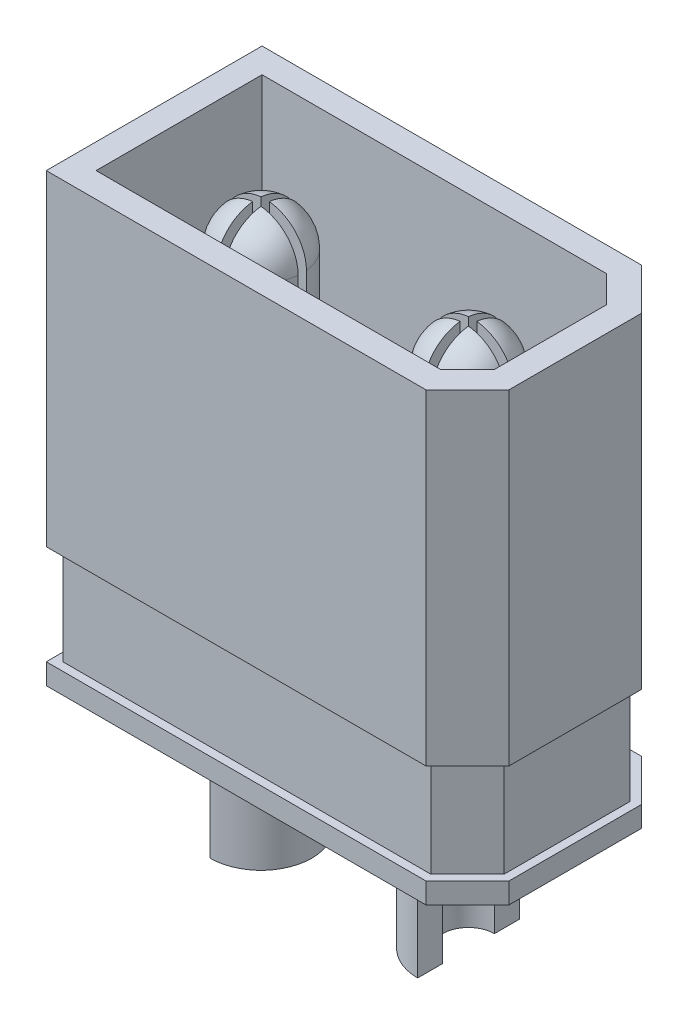
SolidWorks part; units mm, degrees
ref_plane "Front Plane" through (0, 0, 0) normal (0, 0, 1) x (1, 0, 0)
ref_plane "Top Plane" through (0, 0, 0) normal (0, 1, 0) x (1, 0, 0)
ref_plane "Right Plane" through (0, 0, 0) normal (1, 0, 0) x (0, 0, -1)
sketch "Sketch1" plane through (0, 0, 0) normal (0, 1, 0) x (1, 0, 0)
  line L0 (5.075, 1.6) -> (4.075, 2.6)
  line L1 (-5.075, 2.6) -> (5.075, 2.6)
  line L2 (-5.075, 2.6) -> (-5.075, -2.6)
  line L3 (-5.075, -2.6) -> (5.075, -2.6)
  line L4 (5.075, 2.6) -> (5.075, -2.6)
  line L5 (-5.075, 2.6) -> (5.075, -2.6) construction
  line L6 (-5.075, -2.6) -> (5.075, 2.6) construction
  line L7 (-5.075, 0) -> (5.075, 0) construction
  line L8 (5.075, -1.6) -> (4.075, -2.6)
  point P0 (0, 0)
  dimension "D1" = 5.2
  dimension "D2" = 10.15
  dimension "D3" = 1
  dimension "D4" = 45
extrude "Shape" add sketch "Sketch1" along normal blind 10.75 contours L8 L4 L0 L1 L2 L3
sketch "Sketch2" plane through (0, 10.75, 0) normal (0, 1, 0) x (1, 0, 0)
  line L12 (3.8265, -2) -> (4.475, -1.3515)
  line L13 (4.475, -1.3515) -> (4.475, 1.3515)
  line L14 (4.475, 1.3515) -> (3.8265, 2)
  line L15 (3.8265, 2) -> (-4.475, 2)
  line L16 (-4.475, 2) -> (-4.475, -2)
  line L17 (-4.475, -2) -> (3.8265, -2)
  line L18 (3.8265, -2) -> (4.475, -1.3515)
  line L19 (4.475, -1.3515) -> (4.475, 1.3515)
  line L20 (4.475, 1.3515) -> (3.8265, 2)
  line L21 (3.8265, 2) -> (-4.475, 2)
  line L22 (-4.475, 2) -> (-4.475, -2)
  line L23 (-4.475, -2) -> (3.8265, -2)
  dimension "D1" = 0.6
extrude "Cut-Extrude1" cut sketch "Sketch2" against normal blind 6.75
sketch "Sketch3" plane through (0, 4, 0) normal (0, 1, 0) x (1, 0, 0)
  line L0 (-4.475, 0) -> (4.475, 0) construction
  line L1 (-4.475, 2) -> (-4.475, -2) construction
  line L2 (4.475, -1.3515) -> (4.475, 1.3515) construction
  line L3 (0, 2) -> (0, -2) construction
  line L4 (3.8265, 2) -> (-4.475, 2) construction
  line L5 (-4.475, -2) -> (3.8265, -2) construction
  line L7 (1.6754, -1.6) -> (-1.6754, -1.6)
  line L8 (1.6754, -1.6) -> (1.6754, 1.6)
  line L9 (1.6754, 1.6) -> (-1.6754, 1.6)
  line L10 (-1.6754, -1.6) -> (-1.6754, 1.6)
  line L11 (1.6754, -1.6) -> (-1.6754, 1.6) construction
  line L12 (1.6754, 1.6) -> (-1.6754, -1.6) construction
  circle A0 centre (-2.5, 0) radius 1.8
  circle A1 centre (2.5, 0) radius 1.8
  point P15 (0, 0)
  dimension "D2" = 3.6
  dimension "D1" = 5
  dimension "D3" = 3.2
extrude "Cut-Extrude2" cut sketch "Sketch3" against normal up to next contours L7 A1 L9 A0
fillet "Fillet1" radius 0.2 4 edges at (-1.6754, 2, 1.6) (1.6754, 2, 1.6) (1.6754, 2, -1.6) (-1.6754, 2, -1.6)
sketch "Sketch4" plane through (0, 4, 0) normal (0, 1, 0) x (1, 0, 0)
  line L0 (0, 2) -> (0, -2) construction
  line L13 (-4.475, 2) -> (3.8265, 2) construction
  line L14 (-4.475, -2) -> (3.8265, -2) construction
  circle A0 centre (-2.5, 0) radius 1
  circle A2 centre (2.5, 0) radius 1
  dimension "D1" = 2
extrude "Boss-Extrude2" add sketch "Sketch4" along normal offset from surface (6.1 mm away) 0.65 up to face at (1.2755, 10.75, 0)
fillet "Fillet2" radius 1 2 edges at (2.5, 10.1, 1) (-2.5, 10.1, 1)
sketch "Sketch5" plane through (0, 10.75, 0) normal (0, 1, 0) x (1, 0, 0)
  line L0 (0, 2.6) -> (0, -2.6) construction
  line L1 (-2.6, 1) -> (-2.4, 1)
  line L2 (-2.6, 1) -> (-2.6, -1)
  line L3 (-2.6, -1) -> (-2.4, -1)
  line L4 (-2.4, 1) -> (-2.4, -1)
  line L5 (-2.6, 1) -> (-2.4, -1) construction
  line L6 (-2.6, -1) -> (-2.4, 1) construction
  line L7 (-1.5, 0.1) -> (-3.5, 0.1)
  line L8 (-1.5, 0.1) -> (-1.5, -0.1)
  line L9 (-1.5, -0.1) -> (-3.5, -0.1)
  line L10 (-3.5, 0.1) -> (-3.5, -0.1)
  line L11 (-1.5, 0.1) -> (-3.5, -0.1) construction
  line L12 (-1.5, -0.1) -> (-3.5, 0.1) construction
  line L13 (-5.075, 2.6) -> (4.075, 2.6) construction
  line L14 (-5.075, -2.6) -> (4.075, -2.6) construction
  line L15 (1.5, 0.1) -> (1.5, -0.1)
  line L16 (1.5, -0.1) -> (3.5, -0.1)
  line L17 (3.5, 0.1) -> (3.5, -0.1)
  line L18 (1.5, 0.1) -> (3.5, 0.1)
  line L19 (2.6, 1) -> (2.4, 1)
  line L20 (2.4, 1) -> (2.4, -1)
  line L21 (2.6, -1) -> (2.4, -1)
  line L22 (2.6, 1) -> (2.6, -1)
  circle A0 centre (-2.5, 0) radius 1 construction
  point P0 (-2.5, 0)
  point P8 (-2.5, 0)
  dimension "D1" = 0.2
extrude "Cut-Extrude3" cut sketch "Sketch5" against normal up to surface (6.75 mm away) contours L4 L3 L2 L1 | L7 L10 L9 L8 | L16 L17 L18 L15 | L20 L21 L22 L19 up to face at (2.5, 4, 1)
ref_plane "Plane1" through (0, 0.5, 0) normal (0, -1, 0) x (-1, 0, 0)
sketch "Sketch6" plane through (0, 0.5, 0) normal (0, -1, 0) x (-1, 0, 0)
  line L13 (-4.875, -1.5172) -> (-3.9922, -2.4)
  line L14 (-3.9922, -2.4) -> (4.875, -2.4)
  line L15 (4.875, -2.4) -> (4.875, 2.4)
  line L16 (4.875, 2.4) -> (-3.9922, 2.4)
  line L17 (-3.9922, 2.4) -> (-4.875, 1.5172)
  line L18 (-4.875, 1.5172) -> (-4.875, -1.5172)
  line L19 (-4.875, -1.5172) -> (-3.9922, -2.4)
  line L20 (-3.9922, -2.4) -> (4.875, -2.4)
  line L21 (4.875, -2.4) -> (4.875, 2.4)
  line L22 (4.875, 2.4) -> (-3.9922, 2.4)
  line L23 (-3.9922, 2.4) -> (-4.875, 1.5172)
  line L24 (-4.875, 1.5172) -> (-4.875, -1.5172)
  line L25 (-5.075, -1.6) -> (-4.075, -2.6)
  line L26 (-4.075, -2.6) -> (5.075, -2.6)
  line L27 (5.075, -2.6) -> (5.075, 2.6)
  line L28 (5.075, 2.6) -> (-4.075, 2.6)
  line L29 (-4.075, 2.6) -> (-5.075, 1.6)
  line L30 (-5.075, 1.6) -> (-5.075, -1.6)
  line L31 (-5.075, -1.6) -> (-4.075, -2.6)
  line L32 (-4.075, -2.6) -> (5.075, -2.6)
  line L33 (5.075, -2.6) -> (5.075, 2.6)
  line L34 (5.075, 2.6) -> (-4.075, 2.6)
  line L35 (-4.075, 2.6) -> (-5.075, 1.6)
  line L36 (-5.075, 1.6) -> (-5.075, -1.6)
  dimension "D1" = 0.2
  dimension "D2" = 0
extrude "Cut-Extrude4" cut sketch "Sketch6" against normal blind 2.4
sketch "Sketch8" plane through (0, 0, 0) normal (0, -1, 0) x (1, 0, 0)
  line L7 (-4.475, -2) -> (-4.475, 2) construction
  line L8 (3.8265, -2) -> (-4.475, -2) construction
  line L9 (4.475, -1.3515) -> (3.8265, -2) construction
  line L10 (4.475, 1.3515) -> (4.475, -1.3515) construction
  line L11 (3.8265, 2) -> (4.475, 1.3515) construction
  line L12 (-4.475, 2) -> (3.8265, 2) construction
  line L13 (-4.475, -2) -> (-4.475, 2)
  line L14 (3.8265, -2) -> (-4.475, -2)
  line L15 (4.475, -1.3515) -> (3.8265, -2)
  line L16 (4.475, 1.3515) -> (4.475, -1.3515)
  line L17 (3.8265, 2) -> (4.475, 1.3515)
  line L24 (-4.475, 2) -> (3.8265, 2)
extrude "Cut-Extrude5" cut sketch "Sketch8" against normal blind 1
sketch "Sketch7" plane through (0, 1, 0) normal (0, -1, 0) x (1, 0, 0)
  line L0 (0, 1.6) -> (0, -1.6) construction
  line L1 (-1.0717, 1.6) -> (1.0717, 1.6) construction
  line L2 (-1.0717, -1.6) -> (1.0717, -1.6) construction
  circle A0 centre (-2.5, 0) radius 1.225
  arc A1 (-2.4, -0.995) -> (-1.505, -0.1) centre (-2.5, 0) ccw construction
  circle A2 centre (-2.5, 0) radius 0.625
  circle A3 centre (2.5, 0) radius 0.625
  circle A4 centre (2.5, 0) radius 1.225
  dimension "D1" = 0.6
  dimension "D2" = 2.45
extrude "Boss-Extrude3" add sketch "Sketch7" along normal blind 4
sketch "Sketch9" plane through (0, -3, 0) normal (0, -1, 0) x (1, 0, 0)
  line L0 (0, 1.6) -> (0, -1.6) construction
  line L1 (-2.5, 1.225) -> (-3.725, 1.225)
  line L2 (-2.5, 1.225) -> (-2.5, -1.225)
  line L3 (-2.5, -1.225) -> (-3.725, -1.225)
  line L4 (-3.725, 1.225) -> (-3.725, -1.225)
  line L5 (-1.0717, 1.6) -> (1.0717, 1.6) construction
  line L6 (-1.0717, -1.6) -> (1.0717, -1.6) construction
  line L7 (-2.5, 1.225) -> (-2.5, -1.225) construction
  line L8 (2.5, 1.225) -> (3.725, 1.225)
  line L9 (2.5, 1.225) -> (2.5, -1.225)
  line L10 (2.5, -1.225) -> (3.725, -1.225)
  line L11 (3.725, 1.225) -> (3.725, -1.225)
  circle A0 centre (-2.5, 0) radius 1.225 construction
  circle A1 centre (-2.5, 0) radius 1.225 construction
extrude "Cut-Extrude6" cut sketch "Sketch9" against normal blind 2.3
